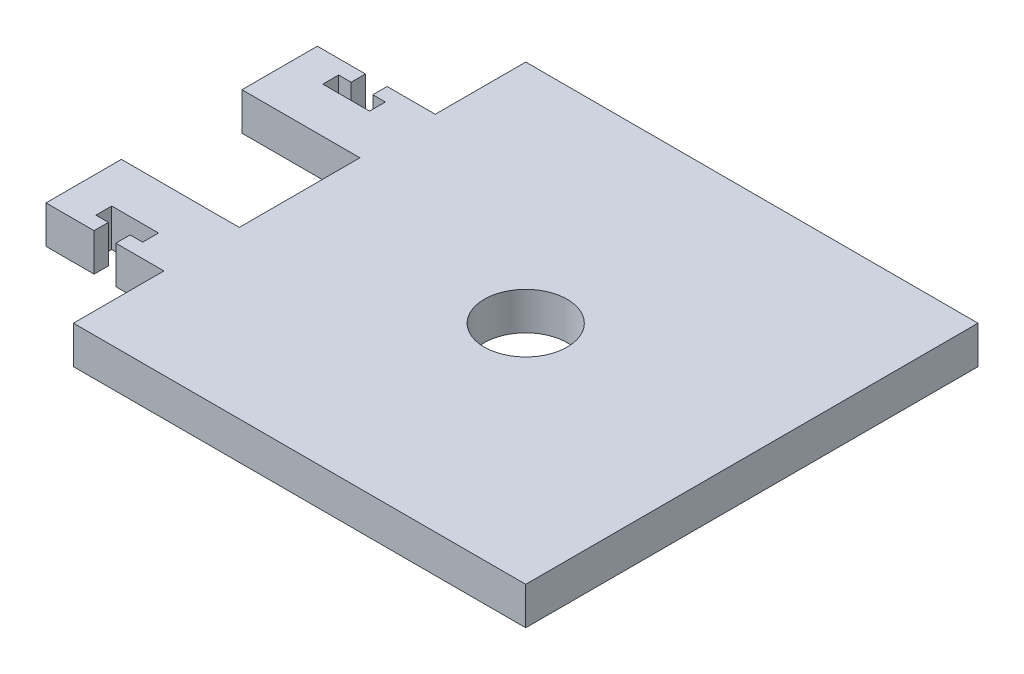
SolidWorks part; units mm, degrees
ref_plane "Front Plane" through (0, 0, 0) normal (0, 0, 1) x (1, 0, 0)
ref_plane "Top Plane" through (0, 0, 0) normal (0, 1, 0) x (1, 0, 0)
ref_plane "Right Plane" through (0, 0, 0) normal (1, 0, 0) x (0, 0, -1)
sketch "Sketch1" plane through (0, 0, 0) normal (0, 1, 0) x (1, 0, 0)
  line L0 (0, 0) -> (38.1, 0) construction
  line L1 (-38.1, -38.1) -> (38.1, -38.1)
  line L2 (-38.1, -38.1) -> (-38.1, -22.86)
  line L3 (-38.1, 38.1) -> (38.1, 38.1)
  line L4 (38.1, -38.1) -> (38.1, 38.1)
  line L5 (-38.1, -38.1) -> (38.1, 38.1) construction
  line L6 (-38.1, 38.1) -> (38.1, -38.1) construction
  line L7 (0, 0) -> (0, -18.5806) construction
  line L8 (-38.1, -22.86) -> (-46.2026, -22.86)
  line L9 (-57.9628, -22.86) -> (-57.9628, -10.16)
  line L10 (-57.9628, -10.16) -> (-38.1, -10.16)
  line L12 (-38.1, 22.86) -> (-46.2026, 22.86)
  line L13 (-57.9628, 10.16) -> (-38.1, 10.16)
  line L14 (-57.9628, 22.86) -> (-57.9628, 10.16)
  line L15 (-38.1, 22.86) -> (-38.1, 38.1)
  line L16 (-38.1, -10.16) -> (-38.1, 10.16)
  line L17 (-48.0314, -24.13) -> (-48.0314, -17.78) construction
  line L19 (-46.2026, -22.86) -> (-46.2026, -20.447)
  line L20 (-46.2026, -20.447) -> (-44.0944, -20.447)
  line L21 (-44.0944, -20.447) -> (-44.0944, -17.78)
  line L22 (-44.0944, -17.78) -> (-51.9684, -17.78)
  line L23 (-49.8602, -22.86) -> (-49.8602, -20.447)
  line L24 (-49.8602, -20.447) -> (-51.9684, -20.447)
  line L25 (-51.9684, -20.447) -> (-51.9684, -17.78)
  line L26 (-49.8602, 20.447) -> (-51.9684, 20.447)
  line L27 (-49.8602, 22.86) -> (-49.8602, 20.447)
  line L28 (-46.2026, 22.86) -> (-46.2026, 20.447)
  line L29 (-46.2026, 20.447) -> (-44.0944, 20.447)
  line L30 (-44.0944, 20.447) -> (-44.0944, 17.78)
  line L31 (-44.0944, 17.78) -> (-51.9684, 17.78)
  line L32 (-51.9684, 20.447) -> (-51.9684, 17.78)
  line L33 (-49.8602, -22.86) -> (-57.9628, -22.86)
  line L34 (-49.8602, 22.86) -> (-57.9628, 22.86)
  circle A0 centre (0, 0) radius 6.985
  point P0 (0, 0)
  point P11 (0, -18.5806)
  point P25 (0, 0)
  point P35 (0, 0)
  dimension "D2" = 13.97
  dimension "D1" = 45
  dimension "D3" = 76.2
  dimension "D4" = 15.24
  dimension "D5" = 20.32
  dimension "D6" = 19.8628
  dimension "D7" = 7.874
  dimension "D8" = 2.667
  dimension "D9" = 5.08
  dimension "D10" = 3.6576
extrude "Boss-Extrude1" add sketch "Sketch1" against normal blind 6.35
